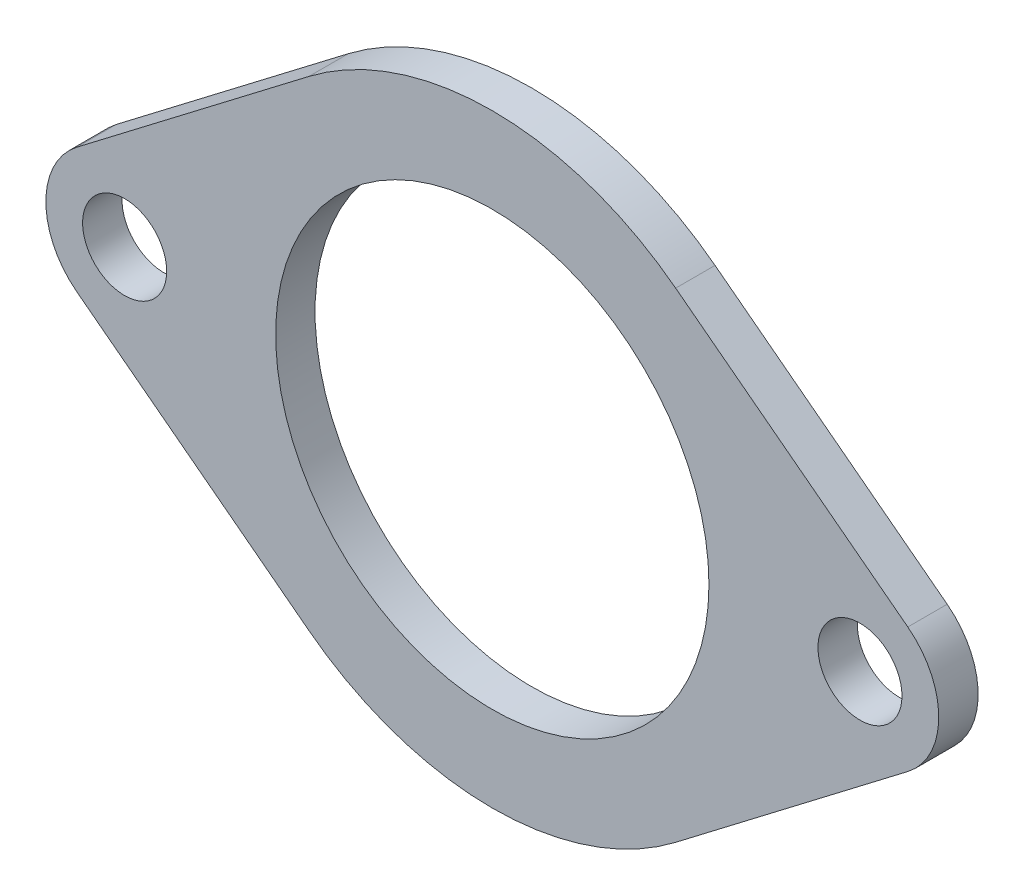
SolidWorks part; units mm, degrees
ref_plane "正面" through (0, 0, 0) normal (0, 0, 1) x (1, 0, 0)
ref_plane "平面" through (0, 0, 0) normal (0, 1, 0) x (1, 0, 0)
ref_plane "右側面" through (0, 0, 0) normal (1, 0, 0) x (0, 0, -1)
sketch "ｽｹｯﾁ1" plane through (0, 0, 0) normal (0, 0, 1) x (1, 0, 0)
  line L0 (-14, 0) -> (14, 0) construction
  line L1 (-15.8214, 2.3838) -> (-6.9821, 9.1378)
  line L2 (6.9821, 9.1378) -> (15.8214, 2.3838)
  line L3 (-6.9821, -9.1378) -> (-15.8214, -2.3838)
  line L4 (6.9821, -9.1378) -> (15.8214, -2.3838)
  circle A0 centre (0, 0) radius 11.5 construction
  circle A1 centre (-14, 0) radius 3 construction
  circle A2 centre (14, 0) radius 3 construction
  arc A3 (-15.8214, -2.3838) -> (-15.8214, 2.3838) centre (-14, 0) cw
  arc A4 (-6.9821, 9.1378) -> (6.9821, 9.1378) centre (0, 0) cw
  arc A5 (-6.9821, -9.1378) -> (6.9821, -9.1378) centre (0, 0) ccw
  arc A6 (15.8214, 2.3838) -> (15.8214, -2.3838) centre (14, 0) cw
  circle A7 centre (0, 0) radius 8.25
  circle A8 centre (-14, 0) radius 1.6
  circle A9 centre (14, 0) radius 1.6
  point P5 (0, 0)
  dimension "D1" = 23
  dimension "D3" = 6
  dimension "D4" = 6
  dimension "D5" = 3.2
  dimension "D6" = 3.2
  dimension "D7" = 16.5
  dimension "D2" = 28
extrude "ﾎﾞｽ - 押し出し1" add sketch "ｽｹｯﾁ1" along normal blind 1.5
